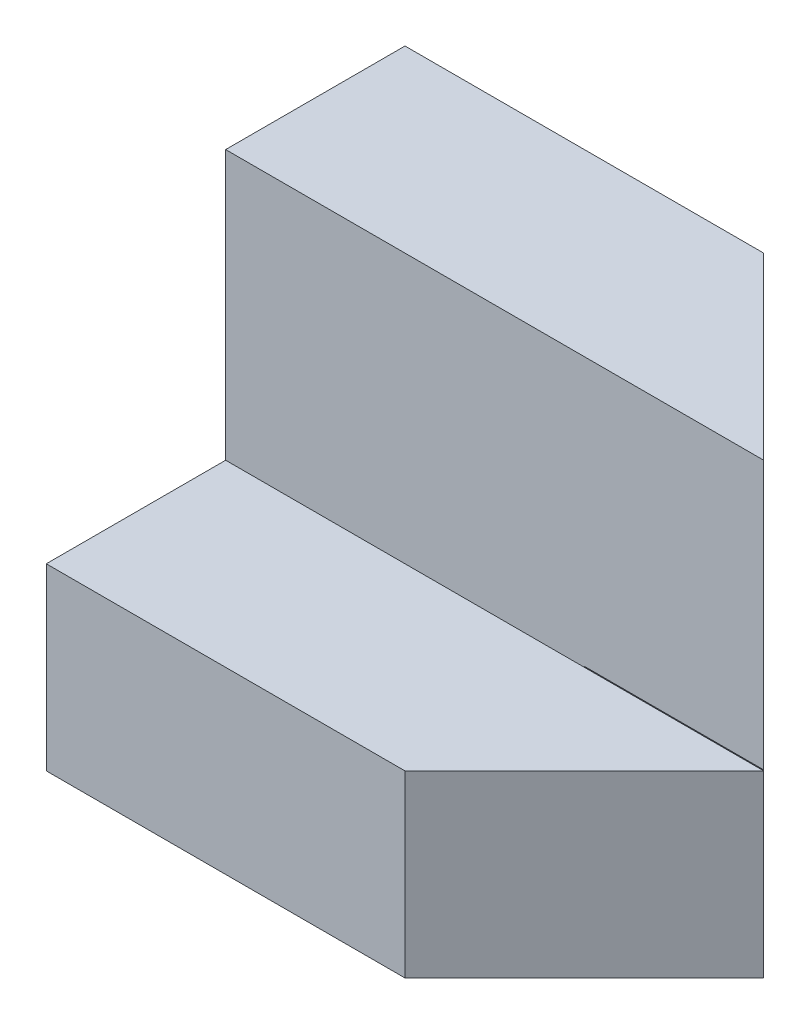
SolidWorks part; units mm, degrees
ref_plane "Front Plane" through (0, 0, 0) normal (0, 0, 1) x (1, 0, 0)
ref_plane "Top Plane" through (0, 0, 0) normal (0, 1, 0) x (1, 0, 0)
ref_plane "Right Plane" through (0, 0, 0) normal (1, 0, 0) x (0, 0, -1)
sketch "Sketch1" plane through (0, 0, 0) normal (0, 0, 1) x (1, 0, 0)
  line L1 (-2, -2.5) -> (2, -2.5)
  line L2 (-2, -2.5) -> (-2, 2.5)
  line L3 (-2, 2.5) -> (2, 2.5)
  line L4 (2, -2.5) -> (2, 2.5)
  line L5 (-2, -2.5) -> (2, 2.5) construction
  line L6 (-2, 2.5) -> (2, -2.5) construction
  point P0 (0, 0)
  dimension "D1" = 5
  dimension "D2" = 4
extrude "Boss-Extrude1" add sketch "Sketch1" along normal blind 2
sketch "Sketch2" plane through (0, 0, 2) normal (0, 0, 1) x (1, 0, 0)
  line L0 (2, -2.5) -> (2, 2.5) construction
  line L1 (-2, -2.5) -> (2, -2.5)
  line L2 (-2, -2.5) -> (-2, -0.5)
  line L3 (-2, -0.5) -> (2, -0.5)
  line L4 (2, -2.5) -> (2, -0.5)
  dimension "D1" = 2
extrude "Boss-Extrude2" add sketch "Sketch2" along normal blind 2
sketch "Sketch3" plane through (0, -0.5, 0) normal (0, 1, 0) x (1, 0, 0)
  line L0 (2, -4) -> (4, -2)
  line L1 (4, -2) -> (2, -2)
  line L2 (2, -2) -> (2, -4)
  dimension "D1" = 2
extrude "Boss-Extrude3" add sketch "Sketch3" against normal blind 2
sketch "Sketch5" plane through (0, 2.5, 0) normal (0, 1, 0) x (1, 0, 0)
  line L0 (2, 0) -> (4, -2)
  line L1 (4, -2) -> (2, -2)
  line L2 (2, -2) -> (2, 0)
extrude "Boss-Extrude5" add sketch "Sketch5" against normal blind 2.99
